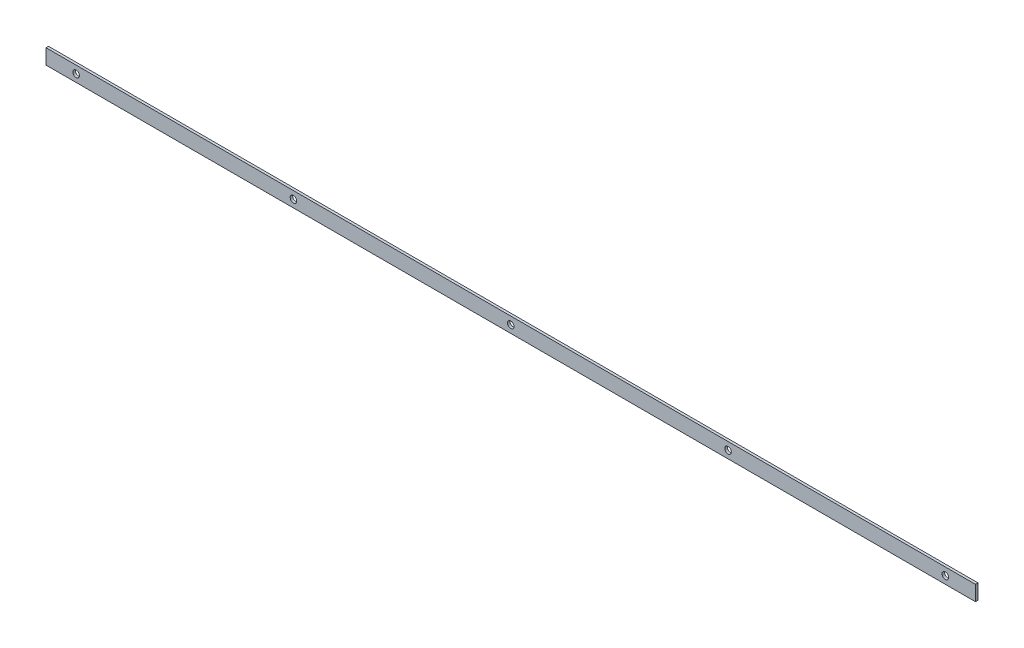
SolidWorks part; units mm, degrees
ref_plane "Plan de face" through (0, 0, 0) normal (0, 0, 1) x (1, 0, 0)
ref_plane "Plan de dessus" through (0, 0, 0) normal (0, 1, 0) x (1, 0, 0)
ref_plane "Plan de droite" through (0, 0, 0) normal (1, 0, 0) x (0, 0, -1)
sketch "Esquisse1" plane through (0, 0, 0) normal (0, 0, 1) x (1, 0, 0)
  line L0 (-925, 0) -> (925, 0)
other "Elément mécano-soudé1"
ref_plane "Plan1" through (-925, 0, 0) normal (1, 0, 0) x (0, 1, 0)
sketch "plat" plane through (-925, 0, 0) normal (1, 0, 0) x (0, 1, 0)
  line L0 (-15, 0) -> (15, 0) construction
  line L1 (-15, 2.5) -> (15, 2.5)
  line L2 (-15, 2.5) -> (-15, -2.5)
  line L3 (-15, -2.5) -> (15, -2.5)
  line L4 (15, 2.5) -> (15, -2.5)
  line L5 (0, 2.5) -> (0, -2.5) construction
  point P8 (0, 0)
  dimension "B" = 30
  dimension "A" = 5
sketch "Esquisse2" plane through (0, 0, -2.5) normal (0, 0, -1) x (-1, 0, 0)
  line L0 (925, 0) -> (-925, 0) construction
  line L1 (925, -15) -> (925, 15) construction
  line L2 (-925, -15) -> (-925, 15) construction
  point P0 (865, 0)
  point P5 (-865, 0)
ref_plane "Plan2" through (865, 0, 0) normal (1, 0, 0) x (0, 0, -1)
hole_wizard "Diamètre du perçage Ø13.0 (13)1" positions "Esquisse3" profile "Esquisse4" hole size "Ø13.0" standard "ISO" end condition through all
sketch "Esquisse3" plane through (0, 0, -2.5) normal (0, 0, -1) x (-1, 0, 0)
  point P0 (865, 0)
sketch "Esquisse4" plane through (-865, 0, -2.5) normal (1, 0, 0) x (0, 1, 0)
  line L0 (0, 0) -> (0, 5)
  line L1 (0, 5) -> (6.5, 5)
  line L2 (6.5, 5) -> (6.5, 0)
  line L5 (6.5, 0) -> (0, 0)
  line L11 (0, -6.35) -> (0, 107.95) construction
  dimension "Diamètre du perçage jusqu'au prochain" = 13
  dimension "Profondeur du perçage jusqu'au prochain" = 5
pattern_linear "Répétition linéaire2" count 5 spacing 432.5 along (1, 0, 0) of "Diamètre du perçage Ø13.0 (13)1"
equation "\"D2@Esquisse2\"=\"D1@Esquisse2\""
